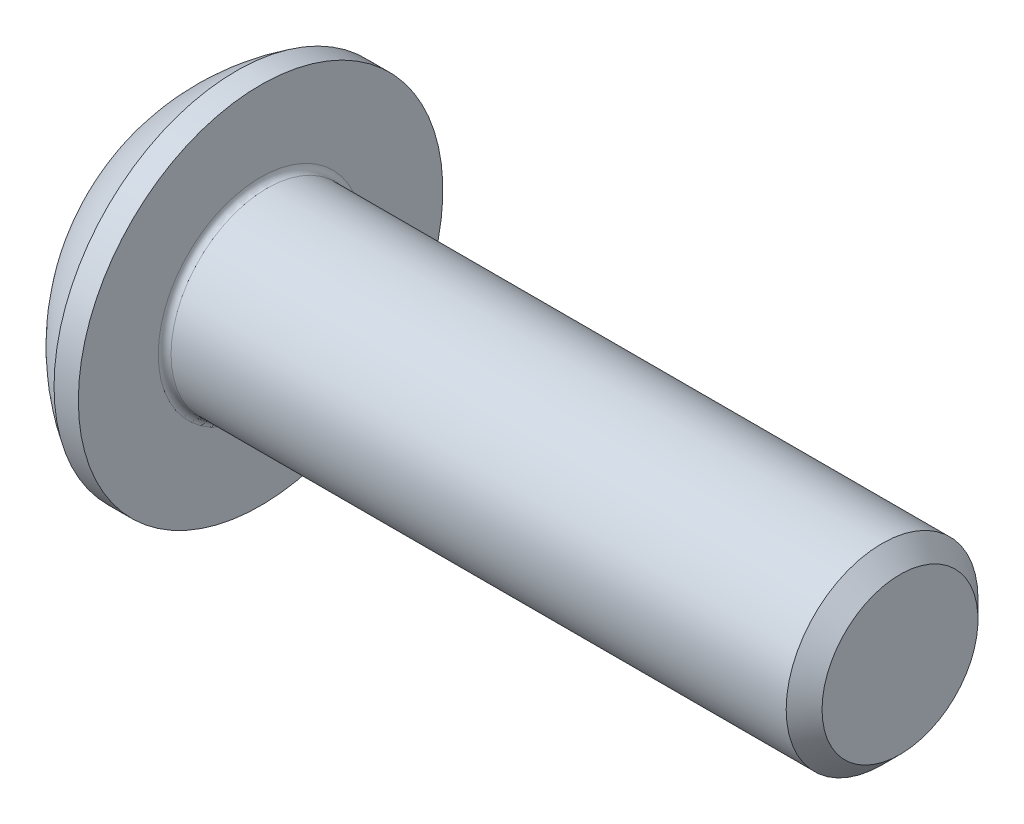
SolidWorks part; units mm, degrees
ref_plane "Plane1" through (0, 0, 0) normal (0, 0, 1) x (1, 0, 0)
ref_plane "Plane2" through (0, 0, 0) normal (0, 1, 0) x (1, 0, 0)
ref_plane "Plane3" through (0, 0, 0) normal (1, 0, 0) x (0, 0, -1)
sketch "BodySke" plane through (0, 0, 0) normal (0, 0, 1) x (1, 0, 0)
  line L0 (11.65, 0) -> (11.65, 1.2195)
  line L1 (11.3695, 1.5) -> (1.65, 1.5)
  line L2 (1.65, 1.5) -> (1.65, 2.85)
  line L3 (1.65, 2.85) -> (1.27, 2.85)
  line L4 (0, 0) -> (101.6, 0) construction
  line L5 (1.65, -2.85) -> (1.27, -2.85) construction
  line L6 (55.6768, -1.5) -> (1.65, -1.5) construction
  line L7 (11.65, 0) -> (0, 0)
  line L8 (0, 1.425) -> (0, -1.425) construction
  line L9 (0, 0) -> (0, 1.425)
  line L10 (11.65, 1.2195) -> (11.3695, 1.5)
  line L11 (11.65, -1.2195) -> (11.3695, -1.5) construction
  line L12 (2.15, 9.525) -> (2.15, -1.5) construction
  line L13 (1.65, 9.525) -> (1.65, -1.5) construction
  arc A1 (0, 1.425) -> (1.27, 2.85) centre (3.0334, 0) cw
  dimension "D1" = 2.85
  dimension "Diameter" = 3
  dimension "Length" = 10
  dimension "Head_dia" = 5.7
  dimension "Head_ht" = 1.65
  dimension "Head_side_ht" = 0.38
  dimension "Minor_dia" = 2.439
  dimension "Body_ch_ang" = 45
  dimension "Advance" = 0.5
  dimension "Thread_nom" = 10
revolve "BaseBody" add sketch "BodySke" angle 360 about L4
cosmetic thread "ThreadCosmetic" parameters "Thread_length"=9, "Thread_minor"=2.439
fillet "Fillet1" radius 0.1 1 edges at (1.65, 0, 1.5)
sketch "Sketch2" plane through (0, 0, 0) normal (0, 0, 1) x (1, 0, 0)
  line L0 (0, 1) -> (1.04, 1)
  line L1 (1.04, 1) -> (1.6174, 0)
  line L3 (1.6174, 0) -> (0, 0)
  line L4 (0, 0) -> (0, 1)
  line L5 (0, -1) -> (1.04, -1) construction
  line L6 (0, 0) -> (47.625, 0) construction
  dimension "D2" = 60
  dimension "PreBroach_depth" = 1.04
  dimension "PreBroach_dia" = 2
revolve "PreBroach" cut sketch "Sketch2" angle 360 about L6
sketch "Sketch3" plane through (0, 0, 0) normal (1, 0, 0) x (0, 0, -1)
  line L0 (-1, -0.5774) -> (-1, 0.5774)
  line L1 (-1, 0.5774) -> (0, 1.1547)
  line L2 (0, 1.1547) -> (1, 0.5774)
  line L3 (1, 0.5774) -> (1, -0.5774)
  line L4 (1, -0.5774) -> (0, -1.1547)
  line L5 (0, -1.1547) -> (-1, -0.5774)
  dimension "D1" = 1
  dimension "D2" = 1
  dimension "D3" = 2
  dimension "Hex_size" = 2
extrude "Hex" cut sketch "Sketch3" along normal blind 1.04
sketch "ThdSchSke" [suppressed] plane through (0, 0, 0) normal (0, 0, 1) x (1, 0, 0)
  line L0 (12.8, -6.8985) -> (12.0287, -8)
  line L1 (12.8, -6.8985) -> (13.5713, -8)
  line L2 (13.5713, -8) -> (13.5713, -10)
  line L3 (-3.175, 0) -> (5.1513, 0) construction
  line L5 (13.5713, -10) -> (12.0287, -10)
  line L6 (12.0287, -10) -> (12.0287, -8)
  dimension "Thread_minor" = 2.439
  dimension "Diameter" = 3
  dimension "Start" = 2.65
  dimension "SideAngle" = 55
  dimension "VeeAngle" = 70
  dimension "Overcut" = 3.75
revolve "ThreadSchematic" [suppressed] cut sketch "ThdSchSke" angle 360 about L3
pattern_linear "ThdSchPat" [suppressed]
equation "\"D1@BodySke\" = \"Head_dia@BodySke\" * .5"
equation "\"Thread_minor@ThreadCosmetic\" = \"Minor_dia@BodySke\""
equation "\"D1@Sketch3\" = \"Hex_size@Sketch3\" / 2"
equation "\"D2@Sketch3\" = \"D1@Sketch3\""
equation "\"D3@Sketch3\" = \"Hex_size@Sketch3\""
equation "\"Thread_length@ThreadCosmetic\" = ((sgn( (\"Length@BodySke\" - \"Advance@BodySke\" * 2.0) - \"Thread_nom@BodySke\" )-1)*( (\"Length@BodySke\" - \"Advance@BodySke\" * 2.0) - \"Thread_nom@BodySke\" ))/-2+ \"Thread_nom@BodySke\""
equation "\"Thread_minor@ThdSchSke\" = \"Minor_dia@BodySke\""
equation "\"Diameter@ThdSchSke\" = \"Diameter@BodySke\""
equation "\"Overcut@ThdSchSke\" = \"Diameter@BodySke\" * 1.25"
equation "\"Start@ThdSchSke\" = \"Head_ht@BodySke\" + \"Length@BodySke\" - \"Thread_length@ThreadCosmetic\"  '---Non-countersunk---"
equation "\"Num_threads@ThdSchPat\" = int( \"Thread_length@ThreadCosmetic\" / \"Advance@BodySke\" + 0.999 )  + 1"
equation "\"Advance@ThdSchPat\" = \"Thread_length@ThreadCosmetic\" /  (\"Num_threads@ThdSchPat\" - 1) 'relax it"
equation "\"Num_threads@ThdSchPat\" = \"Num_threads@ThdSchPat\" - sgn( \"Num_threads@ThdSchPat\" - 1) '---chamfered tips only---"
